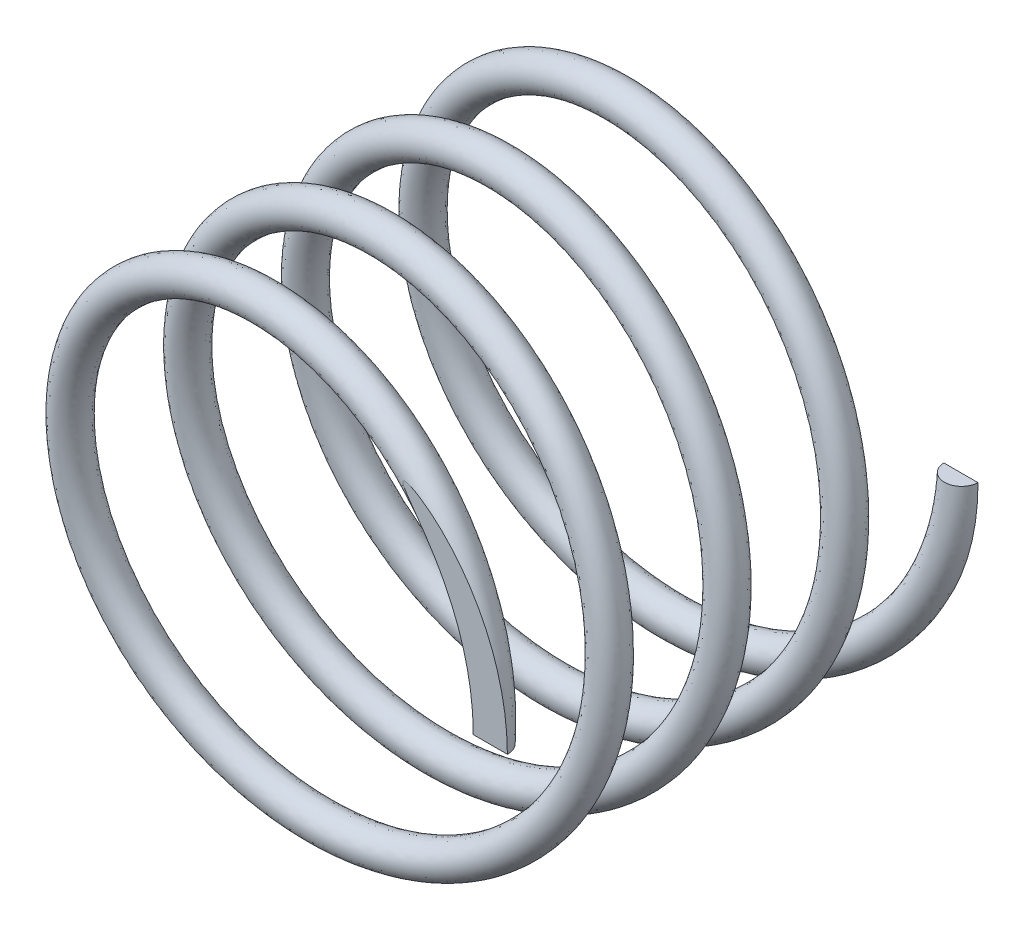
SolidWorks part; units mm, degrees
ref_plane "Front Plane" through (0, 0, 0) normal (0, 0, 1) x (1, 0, 0)
ref_plane "Top Plane" through (0, 0, 0) normal (0, 1, 0) x (1, 0, 0)
ref_plane "Right Plane" through (0, 0, 0) normal (1, 0, 0) x (0, 0, -1)
sketch "Sketch2" plane through (0, 0, 0) normal (0, 0, 1) x (1, 0, 0)
  circle A0 centre (0, 0) radius 28
  dimension "D1" = 56
curve "Helix/Spiral1" pitch 13.75 height 55 turns 4
sketch "Sketch4" plane through (0, 0, 0) normal (0, 1, 0) x (1, 0, 0)
  circle A0 centre (27.9842, -54.9268) radius 2
  spline S0 degree 3 poles (28, 0) (28, -0.1965) (27.3142, -0.5917) (24.3028, -1.1827) (19.5273, -1.7742) (13.3344, -2.3656) (6.1735, -2.957) (-1.4355, -3.5484) (-8.9404, -4.1398) (-15.7962, -4.7312) (-21.5054, -5.3226) (-25.6536, -5.914) (-27.9396, -6.5054) (-28.1975, -7.0968) (-26.4086, -7.6882) (-22.7027, -8.2796) (-17.3489, -8.871) (-10.7357, -9.4624) (-3.3432, -10.0538) (4.2919, -10.6452) (11.6155, -11.2366) (18.0959, -11.828) (23.2628, -12.4194) (26.7411, -13.0108) (28.2782, -13.6022) (27.7627, -14.1935) (25.2319, -14.7849) (20.8696, -15.3763) (14.9924, -15.9677) (8.0269, -16.5591) (0.4787, -17.1505) (-7.1042, -17.7419) (-14.1714, -18.3333) (-20.21, -18.9247) (-24.7815, -19.5161) (-27.5542, -20.1075) (-28.3267, -20.6989) (-27.0431, -21.2903) (-23.7964, -21.8817) (-18.8224, -22.4731) (-12.482, -23.0645) (-5.2357, -23.6559) (2.3908, -24.2473) (9.8436, -24.8387) (16.582, -25.4301) (22.1167, -26.0215) (26.0459, -26.6129) (28.0845, -27.2043) (28.0845, -27.7957) (26.0459, -28.3871) (22.1167, -28.9785) (16.582, -29.5699) (9.8436, -30.1613) (2.3908, -30.7527) (-5.2357, -31.3441) (-12.482, -31.9355) (-18.8224, -32.5269) (-23.7964, -33.1183) (-27.0431, -33.7097) (-28.3267, -34.3011) (-27.5542, -34.8925) (-24.7815, -35.4839) (-20.21, -36.0753) (-14.1714, -36.6667) (-7.1042, -37.2581) (0.4787, -37.8495) (8.0269, -38.4409) (14.9924, -39.0323) (20.8696, -39.6237) (25.2319, -40.2151) (27.7627, -40.8065) (28.2782, -41.3978) (26.7411, -41.9892) (23.2628, -42.5806) (18.0959, -43.172) (11.6155, -43.7634) (4.2919, -44.3548) (-3.3432, -44.9462) (-10.7357, -45.5376) (-17.3489, -46.129) (-22.7027, -46.7204) (-26.4086, -47.3118) (-28.1975, -47.9032) (-27.9396, -48.4946) (-25.6536, -49.086) (-21.5054, -49.6774) (-15.7962, -50.2688) (-8.9404, -50.8602) (-1.4355, -51.4516) (6.1735, -52.043) (13.3344, -52.6344) (19.5273, -53.2258) (24.3028, -53.8173) (27.3142, -54.4083) (28, -54.8035) (28, -55) knots 0 0 0 0 0.010753 0.021505 0.032258 0.043011 0.053763 0.064516 0.075269 0.086022 0.096774 0.107527 0.11828 0.129032 0.139785 0.150538 0.16129 0.172043 0.182796 0.193548 0.204301 0.215054 0.225806 0.236559 0.247312 0.258065 0.268817 0.27957 0.290323 0.301075 0.311828 0.322581 0.333333 0.344086 0.354839 0.365591 0.376344 0.387097 0.397849 0.408602 0.419355 0.430108 0.44086 0.451613 0.462366 0.473118 0.483871 0.494624 0.505376 0.516129 0.526882 0.537634 0.548387 0.55914 0.569892 0.580645 0.591398 0.602151 0.612903 0.623656 0.634409 0.645161 0.655914 0.666667 0.677419 0.688172 0.698925 0.709677 0.72043 0.731183 0.741935 0.752688 0.763441 0.774194 0.784946 0.795699 0.806452 0.817204 0.827957 0.83871 0.849462 0.860215 0.870968 0.88172 0.892473 0.903226 0.913978 0.924731 0.935484 0.946237 0.956989 0.967742 0.978495 0.989247 1 1 1 1 construction
  point P4 (27.9842, -54.9268)
  dimension "D1" = 4
sweep "Sweep1" add profiles "Sketch4" path "Helix/Spiral1"
sketch "Sketch7" plane through (0, 0, 0) normal (0, 0, 1) x (1, 0, 0)
  circle A0 centre (0, 0) radius 41.3455
extrude "Cut-Extrude1" cut sketch "Sketch7" against normal blind 10
ref_plane "Plane2" through (0, 0, 60) normal (0, 0, 1) x (1, 0, 0)
sketch "Sketch9" plane through (0, 0, 60) normal (0, 0, 1) x (1, 0, 0)
  circle A0 centre (0, 0) radius 42.4971
extrude "Cut-Extrude2" cut sketch "Sketch9" against normal blind 5
